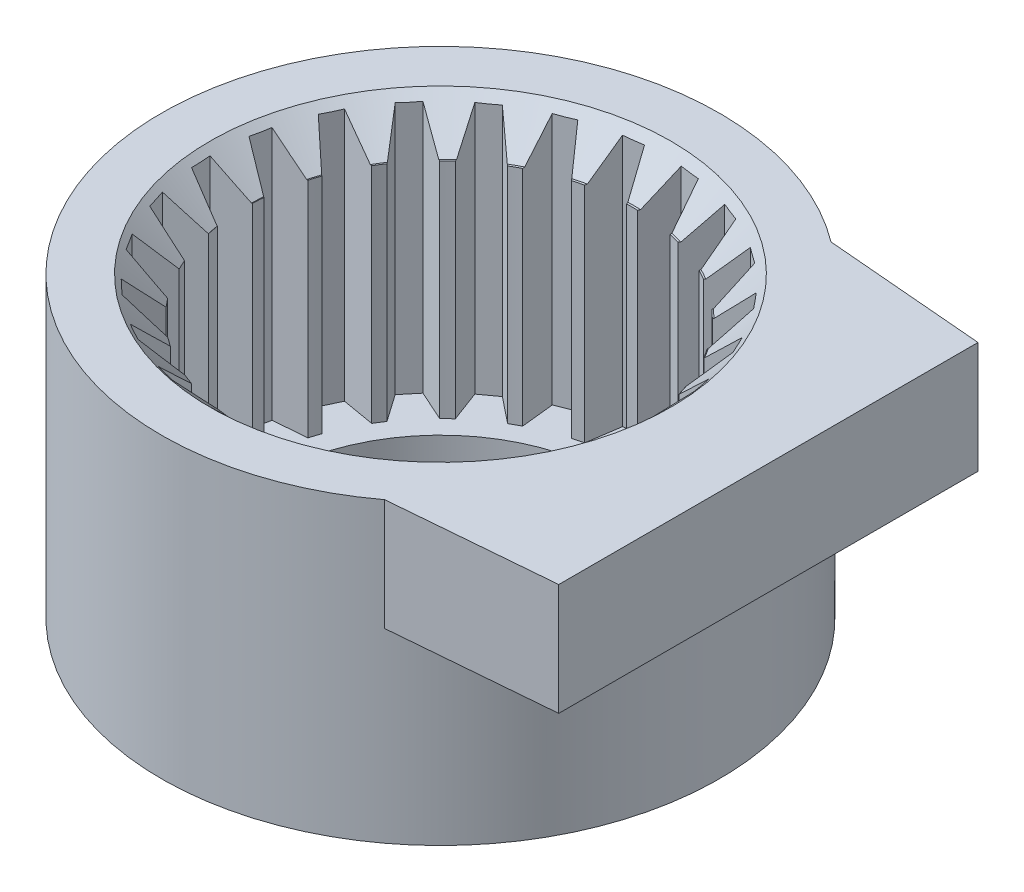
SolidWorks part; units mm, degrees
ref_plane "Front Plane" through (0, 0, 0) normal (0, 0, 1) x (1, 0, 0)
ref_plane "Top Plane" through (0, 0, 0) normal (0, 1, 0) x (1, 0, 0)
ref_plane "Right Plane" through (0, 0, 0) normal (1, 0, 0) x (0, 0, -1)
ref_plane "Plane1" through (0, 4, 0) normal (0, 1, 0) x (1, 0, 0)
sketch "Sketch1" plane through (0, 4, 0) normal (0, 1, 0) x (1, 0, 0)
  line L0 (2.25, -3) -> (4.4078, -2.8177)
  line L1 (4.4078, -2.8177) -> (4.4078, 2.8177)
  line L2 (4.4078, 2.8177) -> (2.25, 3)
  arc A0 (2.25, 3) -> (2.25, -3) centre (0, 0) ccw
extrude "Boss-Extrude1" add sketch "Sketch1" against normal blind 1.5
sketch "Sketch2" plane through (0, 2.5, 0) normal (0, -1, 0) x (1, 0, 0)
  circle A0 centre (0, 0) radius 3.75
extrude "Boss-Extrude2" add sketch "Sketch2" along normal blind 2.5
ref_plane "Plane2" through (0, 0, 0) normal (0, 0, -1) x (-1, 0, 0)
sketch "Sketch3" plane through (0, 0, 0) normal (0, 0, -1) x (-1, 0, 0)
  line L0 (-2.3, 0) -> (0, 0)
  line L1 (0, 0) -> (0, 4)
  line L2 (0, 4) -> (-2.3, 4)
  line L3 (-2.3, 4) -> (-2.3, 3)
  line L4 (-2.3, 3) -> (-1.25, 3)
  line L5 (-1.25, 3) -> (-1.25, 2.5)
  line L6 (-1.25, 2.5) -> (-2.3, 2.5)
  line L7 (-2.3, 2.5) -> (-2.3, 0)
  line L8 (0, 0) -> (0, 4) construction
revolve "Cut-Revolve1" cut sketch "Sketch3" angle 360 about L8
sketch "Sketch5" plane through (0, 4, 0) normal (0, 1, 0) x (1, 0, 0)
  line L0 (-2.5291, -0.5879) -> (-2.9026, -0.8349)
  line L1 (-2.9026, -0.8349) -> (-2.8207, -1.0868)
  line L2 (-2.8207, -1.0868) -> (-2.3734, -1.0671)
  line L3 (-2.3102, -1.2013) -> (-2.6106, -1.5334)
  line L4 (-2.6106, -1.5334) -> (-2.4686, -1.757)
  line L5 (-2.4686, -1.757) -> (-2.0403, -1.6267)
  line L6 (-1.9457, -1.7409) -> (-2.154, -2.1373)
  line L7 (-2.154, -2.1373) -> (-1.9609, -2.3186)
  line L8 (-1.9609, -2.3186) -> (-1.5784, -2.0858)
  line L9 (-1.4585, -2.173) -> (-1.5617, -2.6087)
  line L10 (-1.5617, -2.6087) -> (-1.3295, -2.7363)
  line L11 (-1.3295, -2.7363) -> (-1.0169, -2.4157)
  line L12 (-0.8791, -2.4703) -> (-0.8706, -2.918)
  line L13 (-0.8706, -2.918) -> (-0.6141, -2.9839)
  line L14 (-0.6141, -2.9839) -> (-0.391, -2.5956)
  line L15 (-0.2439, -2.6142) -> (-0.1244, -3.0457)
  line L16 (-0.1244, -3.0457) -> (0.1405, -3.0457)
  line L17 (0.1405, -3.0457) -> (0.2599, -2.6142)
  line L18 (0.4071, -2.5956) -> (0.6301, -2.9839)
  line L19 (0.6301, -2.9839) -> (0.8867, -2.918)
  line L20 (0.8867, -2.918) -> (0.8951, -2.4703)
  line L21 (1.033, -2.4157) -> (1.3456, -2.7363)
  line L22 (1.3456, -2.7363) -> (1.5777, -2.6087)
  line L23 (1.5777, -2.6087) -> (1.4745, -2.173)
  line L24 (1.5945, -2.0858) -> (1.977, -2.3186)
  line L25 (1.977, -2.3186) -> (2.1701, -2.1373)
  line L26 (2.1701, -2.1373) -> (1.9618, -1.7409)
  line L27 (2.0563, -1.6267) -> (2.4847, -1.757)
  line L28 (2.4847, -1.757) -> (2.6266, -1.5334)
  line L29 (2.6266, -1.5334) -> (2.3263, -1.2013)
  line L30 (2.3894, -1.0671) -> (2.8367, -1.0868)
  line L31 (2.8367, -1.0868) -> (2.9186, -0.8349)
  line L32 (2.9186, -0.8349) -> (2.5451, -0.5879)
  line L33 (2.5729, -0.4422) -> (3.0111, -0.3501)
  line L34 (3.0111, -0.3501) -> (3.0277, -0.0857)
  line L35 (3.0277, -0.0857) -> (2.6045, 0.0606)
  line L36 (2.5952, 0.2086) -> (2.9967, 0.4069)
  line L37 (2.9967, 0.4069) -> (2.9471, 0.6671)
  line L38 (2.9471, 0.6671) -> (2.5008, 0.7036)
  line L39 (2.455, 0.8446) -> (2.7946, 1.1365)
  line L40 (2.7946, 1.1365) -> (2.6818, 1.3761)
  line L41 (2.6818, 1.3761) -> (2.2404, 1.3005)
  line L42 (2.161, 1.4257) -> (2.4173, 1.7929)
  line L43 (2.4173, 1.7929) -> (2.2485, 1.9969)
  line L44 (2.2485, 1.9969) -> (1.8398, 1.8139)
  line L45 (1.7317, 1.9155) -> (1.8887, 2.3348)
  line L46 (1.8887, 2.3348) -> (1.6744, 2.4905)
  line L47 (1.6744, 2.4905) -> (1.3241, 2.2116)
  line L48 (1.1941, 2.2831) -> (1.2419, 2.7283)
  line L49 (1.2419, 2.7283) -> (0.9956, 2.8258)
  line L50 (0.9956, 2.8258) -> (0.7257, 2.4685)
  line L51 (0.582, 2.5054) -> (0.5176, 2.9485)
  line L52 (0.5176, 2.9485) -> (0.2548, 2.9817)
  line L53 (0.2548, 2.9817) -> (0.0822, 2.5686)
  line L54 (-0.0661, 2.5686) -> (-0.2388, 2.9817)
  line L55 (-0.2388, 2.9817) -> (-0.5015, 2.9485)
  line L56 (-0.5015, 2.9485) -> (-0.566, 2.5054)
  line L57 (-0.7096, 2.4685) -> (-0.9796, 2.8258)
  line L58 (-0.9796, 2.8258) -> (-1.2259, 2.7283)
  line L59 (-1.2259, 2.7283) -> (-1.1781, 2.2831)
  line L60 (-1.3081, 2.2116) -> (-1.6584, 2.4905)
  line L61 (-1.6584, 2.4905) -> (-1.8727, 2.3348)
  line L62 (-1.8727, 2.3348) -> (-1.7157, 1.9155)
  line L63 (-1.8238, 1.8139) -> (-2.2325, 1.9969)
  line L64 (-2.2325, 1.9969) -> (-2.4013, 1.7929)
  line L65 (-2.4013, 1.7929) -> (-2.145, 1.4257)
  line L66 (-2.2244, 1.3005) -> (-2.6658, 1.3761)
  line L67 (-2.6658, 1.3761) -> (-2.7785, 1.1365)
  line L68 (-2.7785, 1.1365) -> (-2.4389, 0.8446)
  line L69 (-2.4848, 0.7036) -> (-2.9311, 0.6671)
  line L70 (-2.9311, 0.6671) -> (-2.9807, 0.4069)
  line L71 (-2.9807, 0.4069) -> (-2.5792, 0.2086)
  line L72 (-2.5885, 0.0606) -> (-3.0117, -0.0857)
  line L73 (-3.0117, -0.0857) -> (-2.995, -0.3501)
  line L74 (-2.995, -0.3501) -> (-2.5569, -0.4422)
  arc A0 (-2.5569, -0.4422) -> (-2.5291, -0.5879) centre (0.008, -0.0284) ccw
  arc A1 (-2.3734, -1.0671) -> (-2.3102, -1.2013) centre (0.008, -0.0284) ccw
  arc A2 (-2.0403, -1.6267) -> (-1.9457, -1.7409) centre (0.008, -0.0284) ccw
  arc A3 (-1.5784, -2.0858) -> (-1.4585, -2.173) centre (0.008, -0.0284) ccw
  arc A4 (-1.0169, -2.4157) -> (-0.8791, -2.4703) centre (0.008, -0.0284) ccw
  arc A5 (-0.391, -2.5956) -> (-0.2439, -2.6142) centre (0.008, -0.0284) ccw
  arc A6 (0.2599, -2.6142) -> (0.4071, -2.5956) centre (0.008, -0.0284) ccw
  arc A7 (0.8951, -2.4703) -> (1.033, -2.4157) centre (0.008, -0.0284) ccw
  arc A8 (1.4745, -2.173) -> (1.5945, -2.0858) centre (0.008, -0.0284) ccw
  arc A9 (1.9618, -1.7409) -> (2.0563, -1.6267) centre (0.008, -0.0284) ccw
  arc A10 (2.3263, -1.2013) -> (2.3894, -1.0671) centre (0.008, -0.0284) ccw
  arc A11 (2.5451, -0.5879) -> (2.5729, -0.4422) centre (0.008, -0.0284) ccw
  arc A12 (2.6045, 0.0606) -> (2.5952, 0.2086) centre (0.008, -0.0284) ccw
  arc A13 (2.5008, 0.7036) -> (2.455, 0.8446) centre (0.008, -0.0284) ccw
  arc A14 (2.2404, 1.3005) -> (2.161, 1.4257) centre (0.008, -0.0284) ccw
  arc A15 (1.8398, 1.8139) -> (1.7317, 1.9155) centre (0.008, -0.0284) ccw
  arc A16 (1.3241, 2.2116) -> (1.1941, 2.2831) centre (0.008, -0.0284) ccw
  arc A17 (0.7257, 2.4685) -> (0.582, 2.5054) centre (0.008, -0.0284) ccw
  arc A18 (0.0822, 2.5686) -> (-0.0661, 2.5686) centre (0.008, -0.0284) ccw
  arc A19 (-0.566, 2.5054) -> (-0.7096, 2.4685) centre (0.008, -0.0284) ccw
  arc A20 (-1.1781, 2.2831) -> (-1.3081, 2.2116) centre (0.008, -0.0284) ccw
  arc A21 (-1.7157, 1.9155) -> (-1.8238, 1.8139) centre (0.008, -0.0284) ccw
  arc A22 (-2.145, 1.4257) -> (-2.2244, 1.3005) centre (0.008, -0.0284) ccw
  arc A23 (-2.4389, 0.8446) -> (-2.4848, 0.7036) centre (0.008, -0.0284) ccw
  arc A24 (-2.5792, 0.2086) -> (-2.5885, 0.0606) centre (0.008, -0.0284) ccw
  dimension "D1" = 2.598
  dimension "D2" = 2.676
  dimension "D3" = 2.7334
  dimension "D4" = 2.8133
  dimension "D5" = 4.153
  dimension "D6" = 4.3998
  dimension "D7" = 5.2784
  dimension "D8" = 5.2868
  dimension "D9" = 5.5859
  dimension "D10" = 5.7158
  dimension "D11" = 6.9869
  dimension "D12" = 0.2637
  dimension "D13" = 2.9143
extrude "Cut-Extrude1" cut sketch "Sketch5" against normal blind 3.5
sketch "Sketch8" plane through (0, 0, 0) normal (0, 0, 1) x (1, 0, 0)
  line L0 (0, 0) -> (0, 4) construction
  line L1 (55, 4) -> (-55, 4) construction
  line L2 (3.098, 4) -> (0, 4)
  line L3 (0, 4) -> (0, 3.5)
  line L4 (0, 3.5) -> (2.598, 3.5)
  line L5 (2.598, 3.5) -> (3.098, 4)
  line L6 (0, 4) -> (0, 3.5) construction
  point P3 (0, 0)
  point P6 (0, 0)
  point P7 (0, 0)
  point P12 (0, 0)
  point P13 (0, 0)
  dimension "D1" = 3.098
  dimension "D2" = 0.5
  dimension "D3" = 2.598
revolve "Cut-Revolve2" cut sketch "Sketch8" angle 360 about L0
